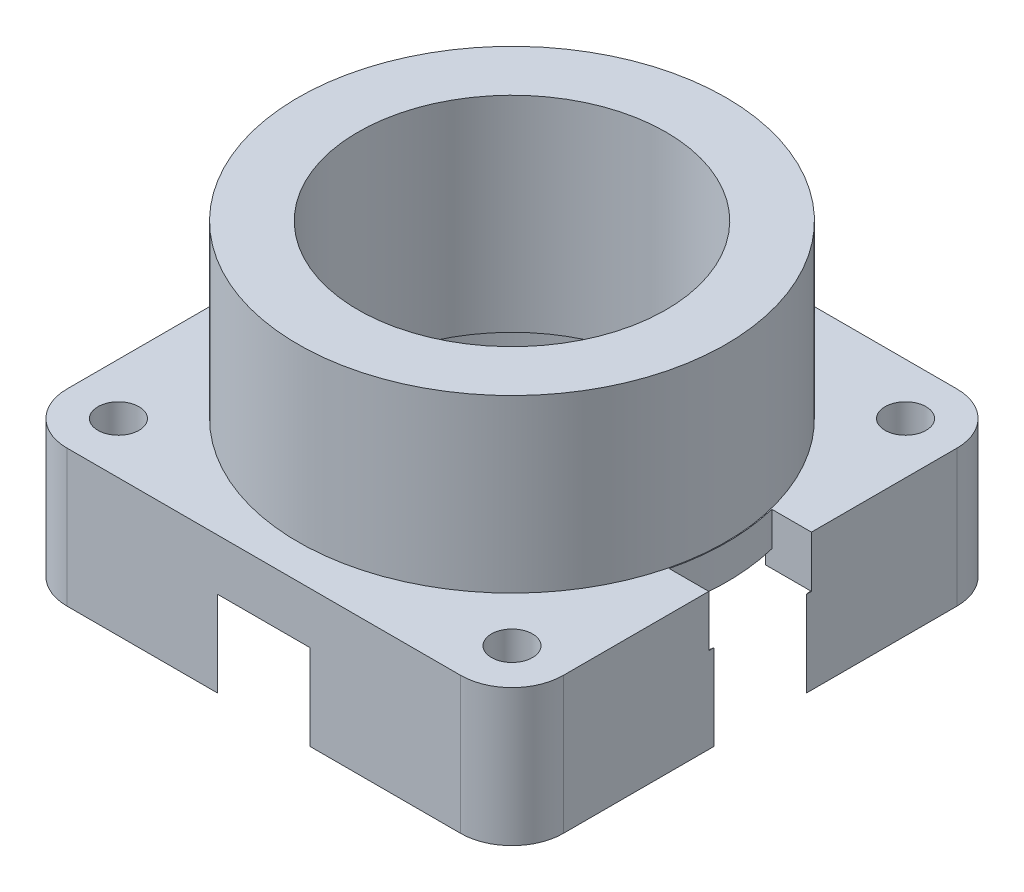
SolidWorks part; units mm, degrees
ref_plane "Front Plane" through (0, 0, 0) normal (0, 0, 1) x (1, 0, 0)
ref_plane "Top Plane" through (0, 0, 0) normal (0, 1, 0) x (1, 0, 0)
ref_plane "Right Plane" through (0, 0, 0) normal (1, 0, 0) x (0, 0, -1)
sketch "Sketch1" plane through (0, 0, 0) normal (0, 1, 0) x (1, 0, 0)
  circle A0 centre (0, 0) radius 12.2
  circle A1 centre (0, 0) radius 13.2
  dimension "D2" = 24.4
  dimension "D1" = 26.4
extrude "Boss-Extrude1" add sketch "Sketch1" against normal blind 2
ref_plane "Plane1" through (0, -2, 0) normal (0, 1, 0) x (1, 0, 0)
sketch "Sketch4" plane through (0, -2, 0) normal (0, 1, 0) x (1, 0, 0)
  circle A0 centre (0, 0) radius 12.2
  circle A1 centre (0, 0) radius 13.2 construction
  circle A2 centre (0, 0) radius 13.2
  dimension "D1" = 24.4
extrude "Boss-Extrude2" add sketch "Sketch4" against normal blind 7
sketch "Sketch13" plane through (0, 0, 0) normal (0, 1, 0) x (1, 0, 0)
  line L0 (10.5357, -3.8) -> (11.5931, -3.8)
  line L1 (11.5931, 3.8) -> (10.5357, 3.8)
  line L2 (-3.8, -10.5357) -> (-3.8, -11.5931)
  line L3 (0, 0) -> (0, 12.2) construction
  line L4 (3.8, -11.5931) -> (3.8, -10.5357)
  line L5 (-3.8, 11.5931) -> (-3.8, 10.5357)
  line L7 (3.8, 10.5357) -> (3.8, 11.5931)
  line L8 (-10.5357, 3.8) -> (-11.5931, 3.8)
  line L9 (-11.5931, -3.8) -> (-10.5357, -3.8)
  circle A0 centre (0, 0) radius 12.2 construction
  arc A2 (3.8, 11.5931) -> (-3.8, 11.5931) centre (0, 0) ccw
  arc A3 (-3.8, 10.5357) -> (3.8, 10.5357) centre (0, 0) cw
  arc A4 (10.5357, 3.8) -> (10.5357, -3.8) centre (0, 0) cw
  arc A5 (11.5931, -3.8) -> (11.5931, 3.8) centre (0, 0) ccw
  arc A6 (3.8, -10.5357) -> (-3.8, -10.5357) centre (0, 0) cw
  arc A7 (-3.8, -11.5931) -> (3.8, -11.5931) centre (0, 0) ccw
  arc A8 (-10.5357, -3.8) -> (-10.5357, 3.8) centre (0, 0) cw
  arc A9 (-11.5931, 3.8) -> (-11.5931, -3.8) centre (0, 0) ccw
  point P25 (0, 0)
  dimension "D6" = 7.6
  dimension "D1" = 1
  dimension "D2" = 4
extrude "Boss-Extrude3" add sketch "Sketch13" against normal blind 1
sketch "Sketch19" plane through (0, -1, 0) normal (0, -1, 0) x (1, 0, 0)
  line L0 (-1.8, 12.0665) -> (-1.8, 11.0544)
  line L1 (1.8, 12.0665) -> (1.8, 11.0544)
  line L2 (-3.8, 10.5357) -> (-3.8, 11.5931) construction
  line L3 (3.8, 11.5931) -> (3.8, 10.5357) construction
  line L4 (12.0665, -1.8) -> (11.0544, -1.8)
  line L5 (12.0665, 1.8) -> (11.0544, 1.8)
  line L6 (-1.8, -12.0665) -> (-1.8, -11.0544)
  line L7 (1.8, -12.0665) -> (1.8, -11.0544)
  line L8 (-12.0665, 1.8) -> (-11.0544, 1.8)
  line L9 (-12.0665, -1.8) -> (-11.0544, -1.8)
  arc A0 (-1.8, 12.0665) -> (1.8, 12.0665) centre (0, 0) cw
  arc A1 (3.8, 11.5931) -> (-3.8, 11.5931) centre (0, 0) ccw construction
  circle A2 centre (0, 0) radius 12.2 construction
  arc A3 (-1.8, 11.0544) -> (1.8, 11.0544) centre (0, 0) cw
  arc A4 (3.8, 10.5357) -> (-3.8, 10.5357) centre (0, 0) ccw construction
  arc A5 (11.0544, 1.8) -> (11.0544, -1.8) centre (0, 0) cw
  arc A6 (12.0665, 1.8) -> (12.0665, -1.8) centre (0, 0) cw
  arc A7 (1.8, -11.0544) -> (-1.8, -11.0544) centre (0, 0) cw
  arc A8 (1.8, -12.0665) -> (-1.8, -12.0665) centre (0, 0) cw
  arc A9 (-11.0544, -1.8) -> (-11.0544, 1.8) centre (0, 0) cw
  arc A10 (-12.0665, -1.8) -> (-12.0665, 1.8) centre (0, 0) cw
  point P34 (0, 0)
  dimension "D1" = 2
  dimension "D2" = 2
  dimension "D3" = 4
extrude "Boss-Extrude4" add sketch "Sketch19" along normal blind 2
sketch "Sketch21" plane through (0, 0, 0) normal (0, 0, 1) x (1, 0, 0)
  line L0 (11.45, 0) -> (13.2, -3)
  line L1 (13.2, 0) -> (-13.2, 0) construction
  line L2 (13.2, -9) -> (13.2, 0) construction
  dimension "D1" = 0.25
  dimension "D2" = 3
sketch "Sketch22" plane through (0, 0, 0) normal (0, 1, 0) x (1, 0, 0)
  line L1 (0, 0) -> (15.957, 0) construction
  arc A2 (10.5357, -3.8) -> (10.5357, 3.8) centre (0, 0) ccw construction
  ellipse E0 centre (11.45, 0) end of major axis (11.45, -1.8) minor radius 1
  dimension "D1" = 1.8
  dimension "D3" = 11.45
  dimension "D2" = 1
ref_plane "Plane3" through (13.2, 0, 0) normal (1, 0, 0) x (0, 0, -1)
sketch "Sketch23" plane through (13.2, 0, 0) normal (1, 0, 0) x (0, 0, -1)
  circle A0 centre (0, -3) radius 1
  dimension "D1" = 2
  dimension "D2" = 3
loft "Cut-Loft4" cut profiles "Sketch22", "Sketch23"
fillet "Fillet2" radius 0.1 1 edges at (13.1947, -3.912, 0.3737)
pattern_circular "CirPattern2" count 2 over 360 of "Cut-Loft4", "Fillet2"
ref_plane "Plane4" through (0, -9, 0) normal (0, 1, 0) x (1, 0, 0)
sketch "Sketch24" plane through (0, -9, 0) normal (0, 1, 0) x (1, 0, 0)
  line L0 (-14.5, 0) -> (14.5, 0) construction
  line L1 (-14.5, 14.5) -> (14.5, 14.5)
  line L2 (-14.5, 14.5) -> (-14.5, -14.5)
  line L3 (-14.5, -14.5) -> (14.5, -14.5)
  line L4 (14.5, 14.5) -> (14.5, -14.5)
  line L5 (0, 14.5) -> (0, 0) construction
  circle A0 centre (0, 0) radius 13.2 construction
  circle A1 centre (0, 0) radius 13.2
  circle A2 centre (-11.5, 11.5) radius 1.2
  circle A3 centre (11.5, 11.5) radius 1.2
  circle A4 centre (11.5, -11.5) radius 1.2
  circle A5 centre (-11.5, -11.5) radius 1.2
  point P10 (0, 0)
  dimension "D3" = 2.4
  dimension "D1" = 29
  dimension "D2" = 29
  dimension "D4" = 11.5
  dimension "D5" = 11.5
extrude "Boss-Extrude5" add sketch "Sketch24" along normal blind 3
sketch "Sketch25" plane through (0, -9, 0) normal (0, 1, 0) x (1, 0, 0)
  line L0 (14.5, 14.5) -> (-14.5, 14.5) construction
  line L1 (14.5, -14.5) -> (14.5, 14.5) construction
  line L2 (-14.5, -14.5) -> (14.5, -14.5) construction
  line L3 (-14.5, 14.5) -> (-14.5, -14.5) construction
  line L4 (14.5, 14.5) -> (2.7042, 14.5)
  line L5 (14.5, -14.5) -> (14.5, -2.7042)
  line L6 (-14.5, -14.5) -> (-2.7042, -14.5)
  line L7 (-14.5, 14.5) -> (-14.5, 2.7042)
  line L8 (2.7042, -14.5) -> (14.5, -14.5)
  line L9 (-14.5, -2.7042) -> (-14.5, -14.5)
  line L10 (-2.7042, 14.5) -> (-14.5, 14.5)
  line L11 (14.5, 2.7042) -> (14.5, 14.5)
  arc A0 (2.7042, -14.5) -> (14.5, -2.7042) centre (0, 0) ccw
  circle A2 centre (-11.5, 11.5) radius 1.2 construction
  circle A3 centre (11.5, 11.5) radius 1.2 construction
  circle A4 centre (11.5, -11.5) radius 1.2 construction
  circle A5 centre (-11.5, -11.5) radius 1.2 construction
  circle A6 centre (-11.5, 11.5) radius 1.2
  circle A7 centre (11.5, 11.5) radius 1.2
  circle A8 centre (11.5, -11.5) radius 1.2
  circle A9 centre (-11.5, -11.5) radius 1.2
  arc A10 (-14.5, -2.7042) -> (-2.7042, -14.5) centre (0, 0) ccw
  arc A11 (-2.7042, 14.5) -> (-14.5, 2.7042) centre (0, 0) ccw
  arc A12 (14.5, 2.7042) -> (2.7042, 14.5) centre (0, 0) ccw
  dimension "D1" = 29.5
extrude "Boss-Extrude6" add sketch "Sketch25" against normal blind 5
fillet "Fillet3" radius 3 4 edges at (14.5, -10, -14.5) (14.5, -10, 14.5) (-14.5, -10, -14.5) (-14.5, -10, 14.5)
sketch "Sketch26" plane through (14.5, 0, 0) normal (1, 0, 0) x (0, 0, -1)
  line L1 (-3, -6) -> (3, -6)
  line L2 (-3, -6) -> (-3, -9)
  line L3 (-3, -9) -> (3, -9)
  line L4 (3, -6) -> (3, -9)
  line L5 (-2.7042, -9) -> (2.7042, -9) construction
  line L7 (-11.5, -6) -> (11.5, -6) construction
  point P10 (0, -6)
  point P11 (0, -6)
  dimension "D1" = 3
  dimension "D2" = 6
extrude "Cut-Extrude1" cut sketch "Sketch26" against normal blind 10
sketch "Sketch27" plane through (0, 0, 0) normal (0, 0, 1) x (1, 0, 0)
  line L1 (-14.8002, 2.2451) -> (14.7103, 2.2451)
  line L2 (-14.8002, 2.2451) -> (-14.8002, -6)
  line L3 (-14.8002, -6) -> (14.7103, -6)
  line L4 (14.7103, 2.2451) -> (14.7103, -6)
extrude "Cut-Extrude2" cut sketch "Sketch27" against normal through all both and the other way through all
sketch "Sketch28" plane through (0, 0, 0) normal (0, 0, 1) x (1, 0, 0)
  line L0 (-12.5493, -6) -> (-12.5493, -8)
  line L2 (-12.5493, -8) -> (-9, -8)
  line L3 (-9, -8) -> (-9, 4)
  line L4 (-9, 4) -> (-12.5, 4)
  line L5 (-12.5, 4) -> (-12.5, -6)
  line L6 (-11.5, -6) -> (11.5, -6) construction
  line L7 (-12.5, -6) -> (-12.5493, -6)
  line L8 (11.8254, -6) -> (-12.2, -6) construction
  line L12 (0, 0) -> (0, 4.1838) construction
  dimension "D1" = 12.5
  dimension "D2" = 9
  dimension "D3" = 2
  dimension "D4" = 10
revolve "Revolve1" add sketch "Sketch28" angle 360 about L12
equation "\"dia_difflayer\"= 13"
equation "\"dia_outer_out\"= 12.5"
equation "\"dia_outer_in\"= 12"
equation "\"dia_inner_out\"= 11"
equation "\"dia_inner_in\"= 10.5"
equation "\"degrees\"= 12.5"
equation "\"d_marker\"= 1"
equation "\"t_marker\"= 0.5"
equation "\"n_markers_1\"= 6"
equation "\"n_markers_2\"= round ( 6 * sin ( 2*\"degrees\" ) / sin ( \"degrees\" ) )"
equation "\"n_markers_3\"= round ( 6 * sin ( 3*\"degrees\" ) / sin ( \"degrees\" ) )"
equation "\"n_markers_4\"= round ( 6 * sin ( 4*\"degrees\" ) / sin ( \"degrees\" ) )"
equation "\"n_markers_5\"= round ( 6 * sin ( 5*\"degrees\" ) / sin ( \"degrees\" ) )"
equation "\"n_teeth\"= 8"
equation "\"tolerance_domes\"= 0.4"
equation "\"tolerance_large\"= 0.4"
equation "\"pinhole_slot\"= 3.8"
equation "\"D6@Sketch13\"=8-\"tolerance_domes\""
equation "\"D2@Sketch1\"=2*\"dia_outer_in\"+\"tolerance_domes\""
equation "\"D1@Sketch1\"=2*\"dia_difflayer\"+\"tolerance_domes\""
equation "\"D1@Sketch4\"=2*\"dia_outer_in\"+\"tolerance_domes\""
